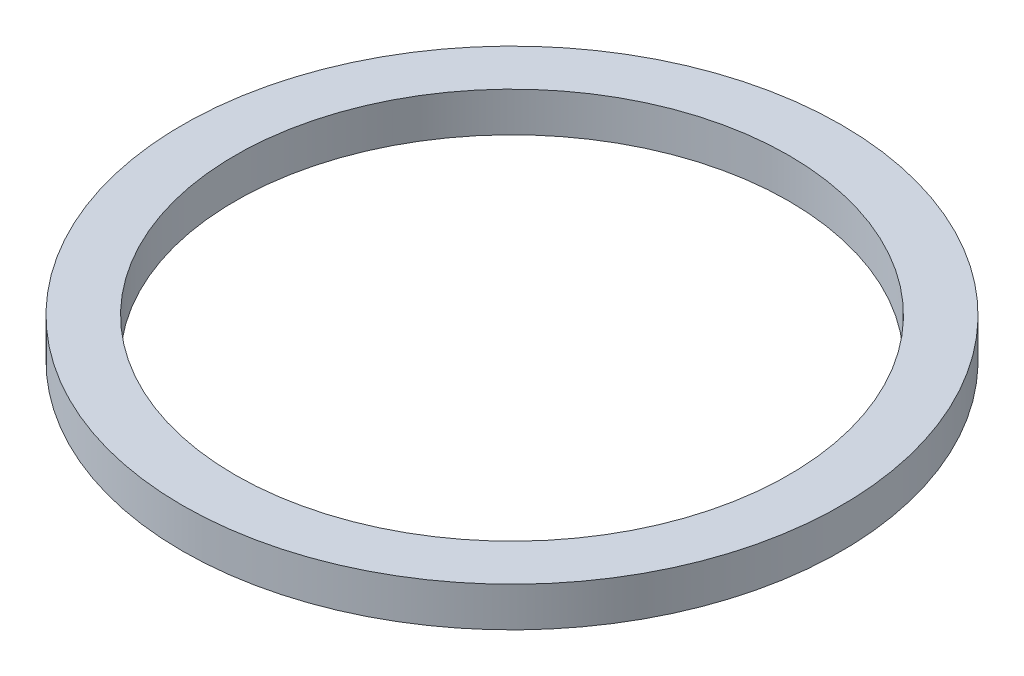
SolidWorks part; units mm, degrees
ref_plane "Plan de face" through (0, 0, 0) normal (0, 0, 1) x (1, 0, 0)
ref_plane "Plan de dessus" through (0, 0, 0) normal (0, 1, 0) x (1, 0, 0)
ref_plane "Plan de droite" through (0, 0, 0) normal (1, 0, 0) x (0, 0, -1)
sketch "Esquisse1" plane through (0, 0, 0) normal (0, 1, 0) x (1, 0, 0)
  circle A0 centre (0, 0) radius 25
  circle A16 centre (0, 0) radius 21
  dimension "D1" = 50
  dimension "D2" = 42
extrude "Boss.-Extru.1" add sketch "Esquisse1" along normal blind 3
